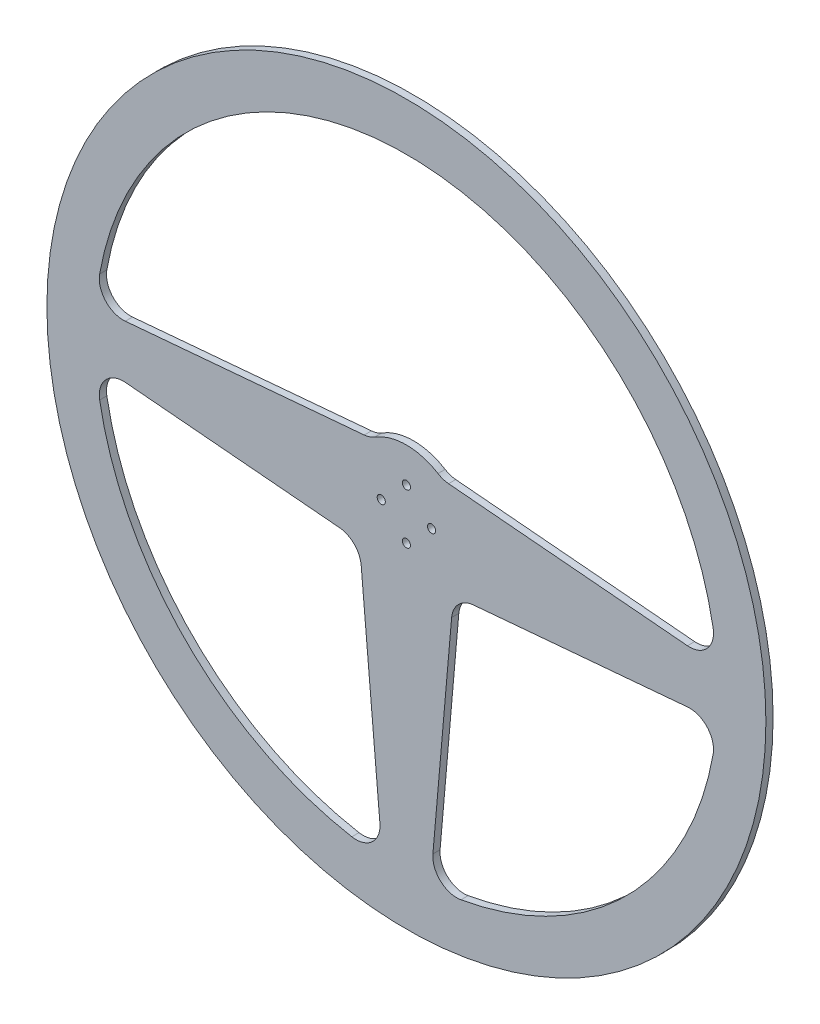
SolidWorks part; units mm, degrees
ref_plane "Alzado" through (0, 0, 0) normal (0, 0, 1) x (1, 0, 0)
ref_plane "Planta" through (0, 0, 0) normal (0, 1, 0) x (1, 0, 0)
ref_plane "Vista lateral" through (0, 0, 0) normal (1, 0, 0) x (0, 0, -1)
sketch "Croquis1" plane through (0, 0, 0) normal (0, 0, 1) x (1, 0, 0)
  line L0 (-1000, 0) -> (49000, 0) construction
  line L1 (-15, 20) -> (-129.6169, 9.9723)
  line L2 (-15, -20) -> (-129.6169, -9.9723)
  line L3 (0, -1000) -> (0, 49000) construction
  line L4 (-20, -15) -> (-9.9723, -129.6169)
  line L5 (20, -15) -> (9.9723, -129.6169)
  line L6 (15, -20) -> (129.6169, -9.9723)
  line L7 (15, 20) -> (129.6169, 9.9723)
  circle A0 centre (0, 0) radius 13 construction
  circle A1 centre (0, 0) radius 150
  circle A2 centre (0, 0) radius 130
  circle A3 centre (0, 0) radius 25
  point P26 (0, 0)
  dimension "D1" = 26
  dimension "D2" = 300
  dimension "D4" = 50
  dimension "D5" = 10
  dimension "D6" = 40
  dimension "D3" = 20
  dimension "D7" = 3
extrude "Saliente-Extruir1" add sketch "Croquis1" along normal blind 3 contours A1 A2 | A3 L1 A2 L2 L4 | A3 L2 L4 A2 L5 L6 | A3 L5 L6 A2 L7 | A3 | A3 L6 L5 | A3 L4 L2
fillet "Redondeo1" radius 10 10 edges at (-9.9723, -129.6169, 1.5) (9.9723, -129.6169, 1.5) (129.6169, -9.9723, 1.5) (129.6169, 9.9723, 1.5) (-129.6169, -9.9723, 1.5) (-129.6169, 9.9723, 1.5) (15, 20, 1.5) (-15, 20, 1.5) (19.5977, -19.5977, 1.5) (-19.5977, -19.5977, 1.5)
hole_wizard "Taladro de margen para M31" positions "Croquis2" profile "Croquis3" hole size "M3" standard "ISO" end condition through all
sketch "Croquis2" plane through (0, 0, 3) normal (0, 0, 1) x (1, 0, 0)
  point P0 (0, 10.5)
  point P9 (10.5, 0)
  point P10 (0, -10.5)
  point P11 (-10.5, 0)
  dimension "D1" = 10.5
  dimension "D2" = 4
sketch "Croquis3" plane through (0, 10.5, 3) normal (1, 0, 0) x (0, -1, 0)
  line L0 (0, 0) -> (0, 3)
  line L1 (0, 3) -> (1.7, 3)
  line L2 (1.7, 3) -> (1.7, 0)
  line L5 (1.7, 0) -> (0, 0)
  line L11 (0, -6.35) -> (0, 107.95) construction
  dimension "Diámetro de taladro hasta el siguiente" = 3.4
  dimension "Profundidad de taladro hasta el siguiente" = 3
